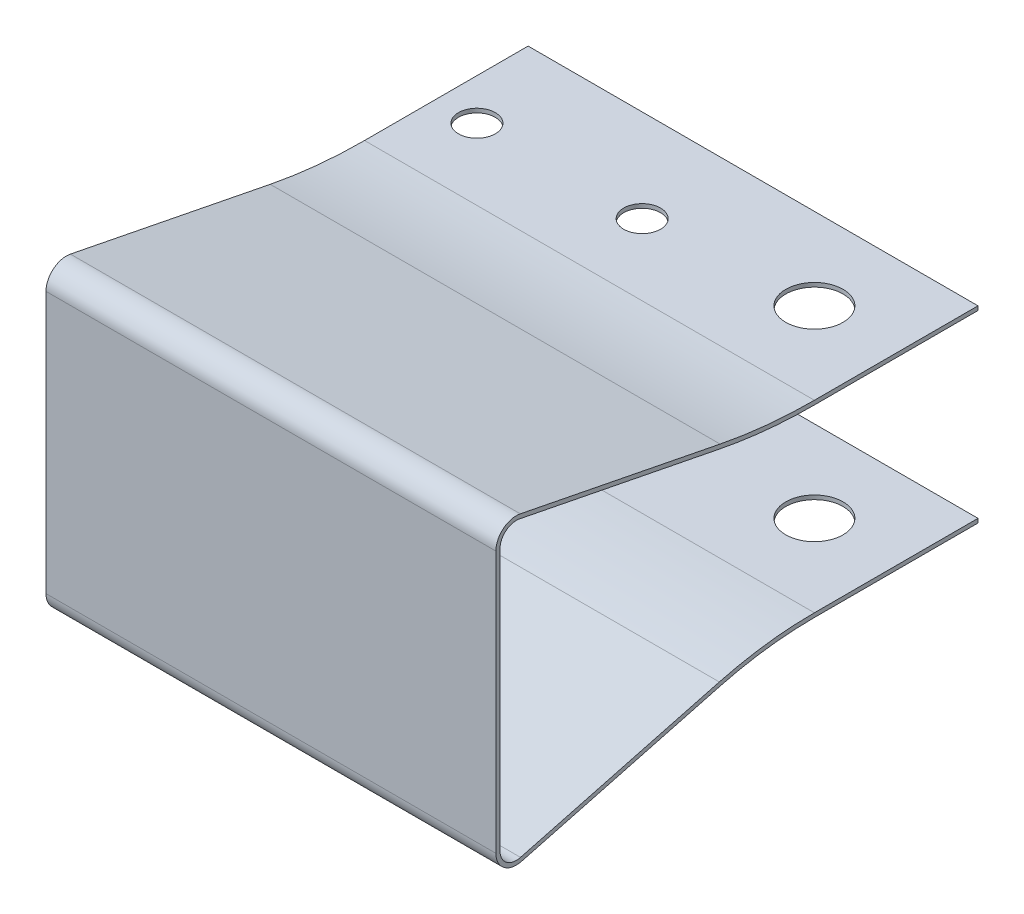
SolidWorks part; units mm, degrees
ref_plane "Front Plane" through (0, 0, 0) normal (0, 0, 1) x (1, 0, 0)
ref_plane "Top Plane" through (0, 0, 0) normal (0, 1, 0) x (1, 0, 0)
ref_plane "Right Plane" through (0, 0, 0) normal (1, 0, 0) x (0, 0, -1)
sketch "Sketch1" plane through (0, 0, 0) normal (1, 0, 0) x (0, 0, -1)
  line L0 (-14.22, 5) -> (-22.22, 5) construction
  line L1 (-24.22, 8) -> (-22.22, 8) construction
  line L2 (-24.22, 8) -> (-24.22, -8) construction
  line L3 (-24.22, -8) -> (-22.22, -8) construction
  line L4 (-14.22, 5) -> (-14.22, 3) construction
  line L5 (-24.22, 8) -> (-14.22, -5) construction
  line L6 (-24.22, -8) -> (-14.22, 5) construction
  line L7 (-22.22, 5) -> (-22.22, 8) construction
  line L8 (-14.22, 3) -> (-21.22, 3) construction
  line L9 (-21.22, 3) -> (-21.22, -3) construction
  line L10 (-21.22, -3) -> (-14.22, -3) construction
  line L11 (-14.22, -5) -> (-22.22, -5) construction
  line L12 (-22.22, -5) -> (-22.22, -8) construction
  line L13 (-14.22, -3) -> (-14.22, -5) construction
  line L14 (-24.22, 8) -> (-24.22, -8)
  line L15 (-10.8136, 6.5687) -> (-23.0262, 8.981)
  line L16 (-5, 5) -> (-5, -5) construction
  line L17 (-5, -5) -> (5, -5) construction
  line L18 (5, 5) -> (5, -5) construction
  line L19 (-5, 5) -> (5, -5) construction
  line L20 (-5, -5) -> (5, 5) construction
  line L21 (-5, 5) -> (5, 5) construction
  line L22 (-5, 5) -> (-5, 6) construction
  line L23 (-5, 6) -> (5, 6) construction
  line L24 (5, 5) -> (5, 6) construction
  line L25 (-10.8136, -5.7553) -> (-22.9645, -8.9668)
  line L26 (-5, -5) -> (5, -5)
  line L27 (-5, 6.25) -> (5, 6.25)
  line L28 (-5, 6) -> (5, 6)
  line L29 (-10.7651, 6.8139) -> (-22.9778, 9.2263)
  line L30 (-24.47, 8) -> (-24.47, -8)
  line L31 (-10.7497, -5.997) -> (-22.9006, -9.2085)
  line L32 (-5, -5.25) -> (5, -5.25)
  line L33 (5, 6.25) -> (5, 6)
  line L34 (5, -5) -> (5, -5.25)
  arc A0 (-24.22, -8) -> (-22.9645, -8.9668) centre (-23.22, -8) ccw
  arc A1 (-23.0262, 8.981) -> (-24.22, 8) centre (-23.22, 8) ccw
  arc A2 (-5, 6.25) -> (-10.7651, 6.8139) centre (-5, 36) cw
  arc A3 (-22.9778, 9.2263) -> (-24.47, 8) centre (-23.22, 8) ccw
  arc A4 (-24.47, -8) -> (-22.9006, -9.2085) centre (-23.22, -8) ccw
  arc A5 (-5, -5.25) -> (-10.7497, -5.997) centre (-5, -27.7512) ccw
  arc A6 (-5, -5) -> (-10.8136, -5.7553) centre (-5, -27.7512) ccw
  arc A7 (-5, 6) -> (-10.8136, 6.5687) centre (-5, 36) cw
  point P0 (-18.0662, 0)
  point P1 (0, 0)
  dimension "D13" = 30
  dimension "D17" = 1
  dimension "D1" = 16
  dimension "D2" = 10
  dimension "D3" = 2
  dimension "D4" = 2
  dimension "D5" = 2
  dimension "D6" = 3
  dimension "D7" = 6
  dimension "D8" = 3
  dimension "D9" = 10
  dimension "D10" = 10
  dimension "D11" = 16.22
  dimension "D12" = 1
  dimension "D14" = 0.25
extrude "Extrude1" add sketch "Sketch1" along normal mid plane 27.5
sketch "Sketch2" plane through (0, 0, 0) normal (0, 1, 0) x (1, 0, 0)
  line L0 (13.75, 5) -> (13.75, -5) construction
  line L1 (13.75, 5) -> (-13.75, 5) construction
  circle A0 centre (8.75, 0) radius 1.75
  circle A1 centre (-1.13, -0.65) radius 1.125
  circle A2 centre (-11.23, -0.65) radius 1.125
  dimension "D1" = 3.5
  dimension "D2" = 2.25
  dimension "D3" = 2.25
  dimension "D4" = 5
  dimension "D5" = 5
  dimension "D6" = 0.65
  dimension "D7" = 14.88
  dimension "D8" = 10.1
extrude "Cut-Extrude1" cut sketch "Sketch2" against normal through all and the other way through all
